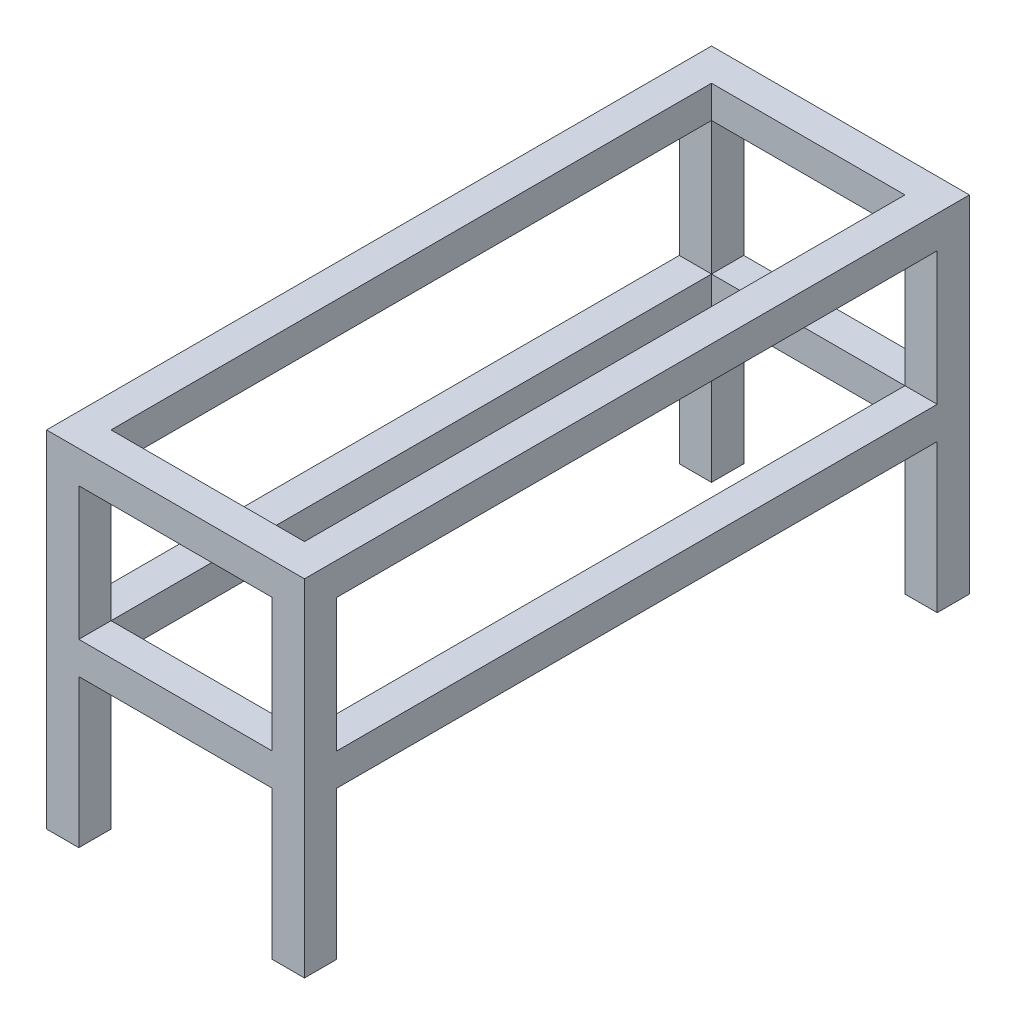
SolidWorks part; units mm, degrees
ref_plane "Front Plane" through (0, 0, 0) normal (0, 0, 1) x (1, 0, 0)
ref_plane "Top Plane" through (0, 0, 0) normal (0, 1, 0) x (1, 0, 0)
ref_plane "Right Plane" through (0, 0, 0) normal (1, 0, 0) x (0, 0, -1)
sketch "Sketch1" plane through (0, 0, 0) normal (0, 0, 1) x (1, 0, 0)
  line L0 (0, 0) -> (640, 0)
  line L3 (560, -857.8016) -> (560, -80)
  line L4 (560, -80) -> (80, -80)
  line L5 (80, -410) -> (560, -410)
  line L6 (0, 0) -> (0, -857.8016)
  line L7 (0, -857.8016) -> (80, -857.8016)
  line L8 (80, -857.8016) -> (80, -80)
  line L11 (320, -88.6285) -> (320, 45.2734) construction
  line L12 (640, -857.8016) -> (560, -857.8016)
  line L13 (640, 0) -> (640, -857.8016)
  line L14 (80, -490) -> (560, -490)
  point P16 (320, 0)
  point P23 (320, -80)
extrude "Boss-Extrude1" add sketch "Sketch1" against normal blind 80 contours L8 L14 L3 L5 | L4 L11 L0 L6 L7 L8 | L11 L4 L3 L12 L13 L0
sketch "Sketch2" plane through (0, 0, -80) normal (0, 0, -1) x (-1, 0, 0)
  line L0 (-640, 0) -> (-640, -857.8016) construction
  line L1 (-640, 0) -> (-560, 0)
  line L2 (-640, 0) -> (-640, -80)
  line L3 (-640, -80) -> (-560, -80)
  line L4 (-560, 0) -> (-560, -80)
  line L5 (-80, -80) -> (0, -80)
  line L6 (-80, -80) -> (-80, 0)
  line L7 (-80, 0) -> (0, 0)
  line L8 (0, -80) -> (0, 0)
  line L9 (-560, -410) -> (-640, -410)
  line L10 (-560, -410) -> (-560, -490)
  line L11 (-560, -490) -> (-640, -490)
  line L12 (-640, -410) -> (-640, -490)
  line L16 (0, 0) -> (0, -857.8016) construction
  line L18 (-80, -490) -> (0, -490)
  line L19 (-80, -490) -> (-80, -410)
  line L20 (-80, -410) -> (0, -410)
  line L21 (0, -490) -> (0, -410)
extrude "Boss-Extrude2" add sketch "Sketch2" along normal blind 745
ref_plane "Plane2" through (0, 0, -825) normal (0, 0, 1) x (1, 0, 0)
mirror "Mirror2" about plane through (0, 0, -825) normal (0, 0, 1) of "Boss-Extrude2"
mirror "Mirror3" about plane through (0, 0, -825) normal (0, 0, 1) of "Boss-Extrude1"
